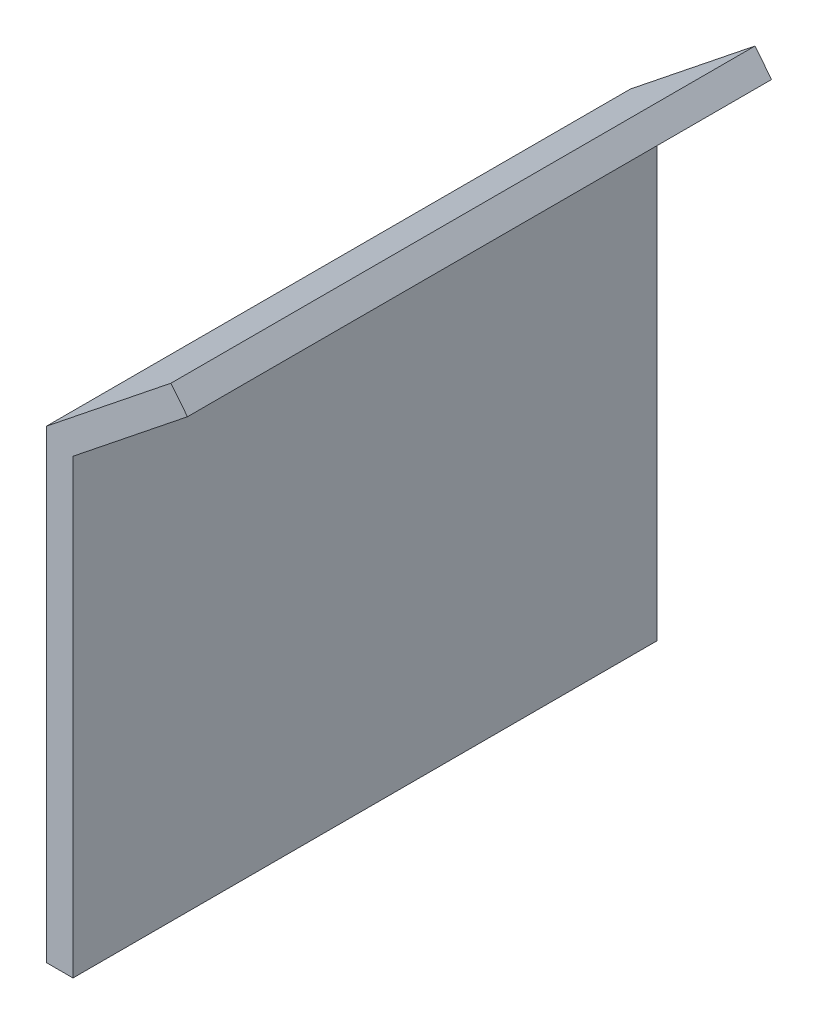
SolidWorks part; units mm, degrees
ref_plane "Front Plane" through (0, 0, 0) normal (0, 0, 1) x (1, 0, 0)
ref_plane "Top Plane" through (0, 0, 0) normal (0, 1, 0) x (1, 0, 0)
ref_plane "Right Plane" through (0, 0, 0) normal (1, 0, 0) x (0, 0, -1)
sketch "Sketch1" plane through (0, 0, 0) normal (0, 0, 1) x (1, 0, 0)
  line L0 (-95.841, 50.453) -> (-95.841, 84.4909)
  line L1 (-95.841, 84.4909) -> (-87.2172, 91.3804)
  line L2 (-87.2172, 91.3804) -> (-88.4655, 92.943)
  line L3 (-88.4655, 92.943) -> (-97.841, 85.453)
  line L4 (-97.841, 85.453) -> (-97.841, 50.453)
  line L5 (-97.841, 50.453) -> (-95.841, 50.453)
  dimension "D1" = 2
  dimension "D2" = 2
  dimension "D3" = 35
  dimension "D4" = 12
extrude "Boss-Extrude1" add sketch "Sketch1" along normal up to surface (44 mm away)
